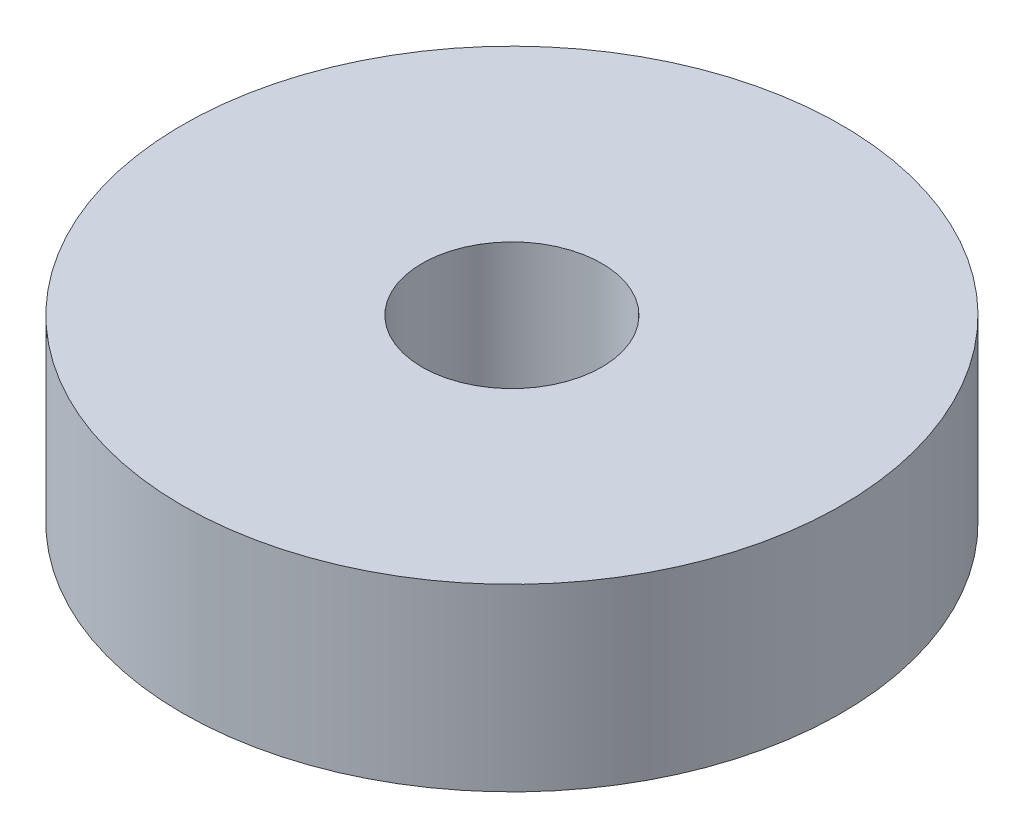
SolidWorks part; units mm, degrees
ref_plane "Front Plane" through (0, 0, 0) normal (0, 0, 1) x (1, 0, 0)
ref_plane "Top Plane" through (0, 0, 0) normal (0, 1, 0) x (1, 0, 0)
ref_plane "Right Plane" through (0, 0, 0) normal (1, 0, 0) x (0, 0, -1)
sketch "Sketch1" plane through (0, 0, 0) normal (0, 1, 0) x (1, 0, 0)
  circle A0 centre (0, 0) radius 3
  circle A1 centre (0, 0) radius 11
  dimension "D1" = 6
  dimension "D2" = 22
extrude "Boss-Extrude1" add sketch "Sketch1" along normal blind 6
